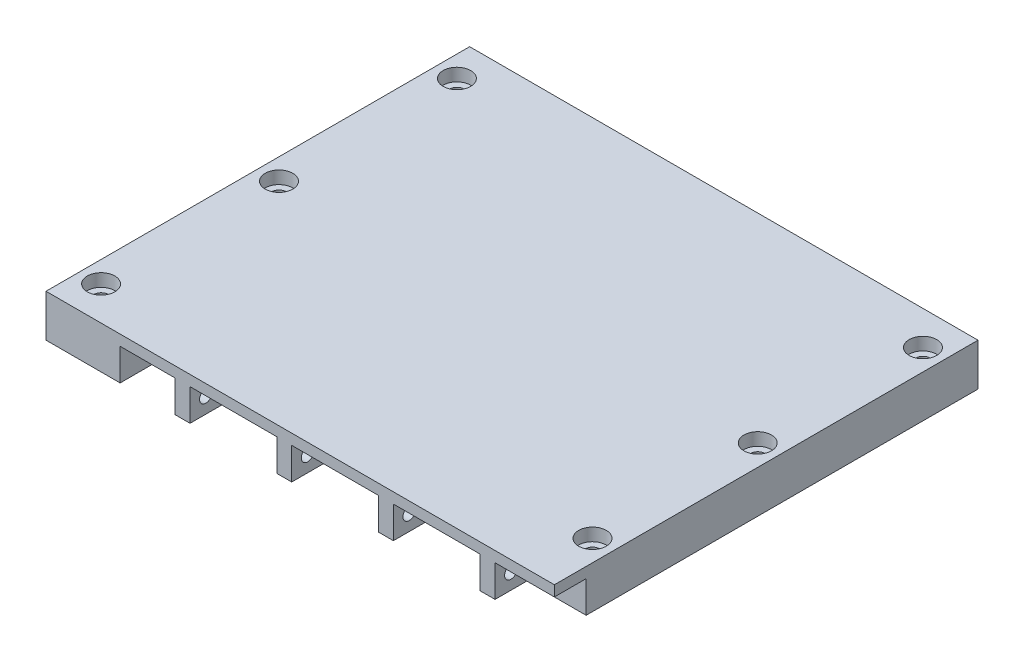
SolidWorks part; units mm, degrees
ref_plane "Front Plane" through (0, 0, 0) normal (0, 0, 1) x (1, 0, 0)
ref_plane "Top Plane" through (0, 0, 0) normal (0, 1, 0) x (1, 0, 0)
ref_plane "Right Plane" through (0, 0, 0) normal (1, 0, 0) x (0, 0, -1)
sketch "Sketch1" plane through (0, 0, 0) normal (0, 1, 0) x (1, 0, 0)
  line L1 (60, -50) -> (-60, -50)
  line L2 (60, -50) -> (60, 50)
  line L3 (60, 50) -> (-60, 50)
  line L4 (-60, -50) -> (-60, 50)
  line L5 (60, -50) -> (-60, 50) construction
  line L6 (60, 50) -> (-60, -50) construction
  point P0 (0, 0)
  dimension "D1" = 120
  dimension "D2" = 100
extrude "Boss-Extrude1" add sketch "Sketch1" along normal blind 10
sketch "Sketch2" plane through (0, 0, 50) normal (0, 0, 1) x (1, 0, 0)
  line L0 (-60, 0) -> (60, 0) construction
  line L4 (-29.5, -7.5) -> (-42.5, -7.5)
  line L5 (-29.5, -7.5) -> (-29.5, 7.5)
  line L6 (-29.5, 7.5) -> (-42.5, 7.5)
  line L7 (-42.5, -7.5) -> (-42.5, 7.5)
  line L8 (-29.5, -7.5) -> (-42.5, 7.5) construction
  line L9 (-29.5, 7.5) -> (-42.5, -7.5) construction
  line L10 (-5.5, -7.5) -> (-18.5, -7.5)
  line L11 (-5.5, -7.5) -> (-5.5, 7.5)
  line L12 (-5.5, 7.5) -> (-18.5, 7.5)
  line L13 (-18.5, -7.5) -> (-18.5, 7.5)
  line L14 (-5.5, -7.5) -> (-18.5, 7.5) construction
  line L15 (-5.5, 7.5) -> (-18.5, -7.5) construction
  line L16 (18.5, -7.5) -> (5.5, -7.5)
  line L17 (18.5, -7.5) -> (18.5, 7.5)
  line L18 (18.5, 7.5) -> (5.5, 7.5)
  line L19 (5.5, -7.5) -> (5.5, 7.5)
  line L20 (18.5, -7.5) -> (5.5, 7.5) construction
  line L21 (18.5, 7.5) -> (5.5, -7.5) construction
  line L22 (42.5, -7.5) -> (29.5, -7.5)
  line L23 (42.5, -7.5) -> (42.5, 7.5)
  line L24 (42.5, 7.5) -> (29.5, 7.5)
  line L25 (29.5, -7.5) -> (29.5, 7.5)
  line L26 (42.5, -7.5) -> (29.5, 7.5) construction
  line L27 (42.5, 7.5) -> (29.5, -7.5) construction
  line L29 (60, 0) -> (-60, 0) construction
  point P7 (-36, 0)
  point P8 (-12, 0)
  point P9 (12, 0)
  point P10 (36, 0)
  point P11 (-36, 0)
  point P16 (-12, 0)
  point P21 (12, 0)
  point P26 (36, 0)
  point P33 (0, 0)
  dimension "D1" = 120
  dimension "D3" = 13
  dimension "D4" = 15
extrude "Cut-Extrude1" cut sketch "Sketch2" against normal blind 35
sketch "Sketch3" plane through (0, 0, 50) normal (0, 0, 1) x (1, 0, 0)
  line L0 (60, 10) -> (60, 0) construction
  line L1 (-18.5, 0) -> (-26, 0)
  line L2 (-18.5, 0) -> (-18.5, 7.5)
  line L3 (-18.5, 7.5) -> (-26, 7.5)
  line L4 (-26, 0) -> (-26, 7.5)
  line L5 (5.5, 0) -> (-2, 0)
  line L6 (5.5, 0) -> (5.5, 7.5)
  line L7 (5.5, 7.5) -> (-2, 7.5)
  line L8 (-2, 0) -> (-2, 7.5)
  line L9 (29.5, 0) -> (22, 0)
  line L10 (29.5, 0) -> (29.5, 7.5)
  line L11 (29.5, 7.5) -> (22, 7.5)
  line L12 (22, 0) -> (22, 7.5)
  line L13 (46, 0) -> (60, 0)
  line L14 (46, 0) -> (46, 7.5)
  line L15 (46, 7.5) -> (60, 7.5)
  line L16 (60, 0) -> (60, 7.5)
  line L17 (60, 0) -> (42.5, 0) construction
  line L18 (5.5, 7.5) -> (5.5, 0) construction
  line L19 (5.5, 0) -> (-5.5, 0) construction
  line L20 (-5.5, 7.5) -> (-18.5, 7.5) construction
  line L21 (-29.5, 0) -> (-29.5, 7.5) construction
  line L22 (-5.5, 0) -> (-5.5, 7.5) construction
  line L23 (42.5, 0) -> (42.5, 7.5) construction
  line L24 (18.5, 0) -> (18.5, 7.5) construction
  line L25 (-18.5, 0) -> (-5.5, 0) construction
  line L26 (-18.5, 7.5) -> (-18.5, 0) construction
  line L27 (18.5, 7.5) -> (5.5, 7.5) construction
  line L28 (42.5, 7.5) -> (29.5, 7.5) construction
  dimension "D1" = 3.5
  dimension "D2" = 3.5
  dimension "D3" = 3.5
  dimension "D4" = 3.5
extrude "Cut-Extrude2" cut sketch "Sketch3" against normal blind 7.5
sketch "Sketch4" plane through (46, 0, 0) normal (1, 0, 0) x (0, 0, -1)
  line L1 (-42.5, 0) -> (-50, 0) construction
  line L2 (-50, 10) -> (-50, 7.5) construction
  circle A0 centre (-46.25, 3.75) radius 1.5
  dimension "D1" = 3
  dimension "D2" = 3.75
  dimension "D3" = 3.75
extrude "Cut-Extrude3" cut sketch "Sketch4" against normal up to surface (75.5 mm away) up to face at (-29.5, 3.75, 32.5)
hole_wizard "CBORE for M3 SHCS" positions "Sketch7" profile "Sketch8" counterbore size "M3" standard "ANSI Metric"
sketch "Sketch7" plane through (-676.2935, 10, -1323.2827) normal (0, 1, 0) x (1, 0, 0)
  line L3 (621.2935, -1281.2827) -> (621.2935, -1365.2827) construction
  line L5 (731.2935, -1281.2827) -> (731.2935, -1359.2827) construction
  circle A0 centre (731.2935, -1281.2827) radius 2.243
  circle A1 centre (731.2935, -1359.2827) radius 2.2384
  circle A3 centre (621.2935, -1281.2827) radius 2.3325
  circle A4 centre (621.2935, -1365.2827) radius 1.7576
  circle A5 centre (621.2935, -1323.2827) radius 1.8624
  circle A6 centre (731.2935, -1320.2827) radius 2.0271
  point P1 (731.2935, -1281.2827)
  point P8 (731.2935, -1359.2827)
  point P15 (621.2935, -1281.2827)
  point P17 (621.2935, -1365.2827)
  point P19 (621.2935, -1323.2827)
  point P27 (731.2935, -1320.2827)
sketch "Sketch8" plane through (55, 10, -42) normal (1, 0, 0) x (0, 0, 1)
  line L0 (0, 0) -> (0, 24.0215)
  line L1 (0, 24.0215) -> (1.7, 23)
  line L2 (1.7, 23) -> (1.7, 3)
  line L3 (1.7, 3) -> (3.25, 3)
  line L4 (3.25, 3) -> (3.25, 0)
  line L5 (3.25, 0) -> (0, 0)
  line L6 (0, 24.0215) -> (-1.7, 23) construction
  line L7 (0, -6.35) -> (0, 107.95) construction
  dimension "Hole Dia." = 3.4
  dimension "Hole Depth" = 23
  dimension "C'Bore Dia." = 6.5
  dimension "C'Bore Depth" = 3
  dimension "Drill Angle" = 118
